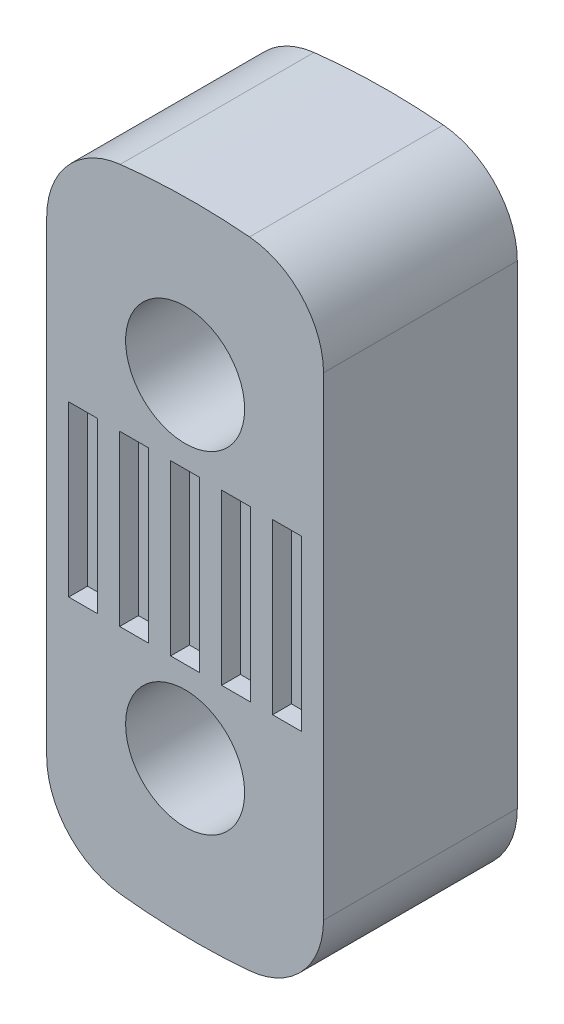
SolidWorks part; units mm, degrees
ref_plane "Front Plane" through (0, 0, 0) normal (0, 0, 1) x (1, 0, 0)
ref_plane "Top Plane" through (0, 0, 0) normal (0, 1, 0) x (1, 0, 0)
ref_plane "Right Plane" through (0, 0, 0) normal (1, 0, 0) x (0, 0, -1)
sketch "Sketch1" plane through (0, 0, 0) normal (0, 0, 1) x (1, 0, 0)
  line L0 (-34.3488, 6) -> (10.6512, 6) construction
  line L8 (-5, 14.4344) -> (-5, -2.4344)
  line L9 (5, 14.563) -> (5, -2.563)
  arc A0 (-2.3438, 17.4132) -> (-5, 14.4344) centre (-2.0016, 14.4344) ccw
  circle A1 centre (0, 0) radius 2.15
  arc A3 (0.0452, -5.5638) -> (-2.3438, -5.4132) centre (0.3138, 17.7221) cw
  arc A5 (5, 14.563) -> (2.3268, 17.4782) centre (2.0739, 14.563) ccw
  circle A6 centre (0, 12) radius 2.15
  arc A7 (2.3268, -5.4782) -> (0.0452, -5.5638) centre (0.3138, 17.7221) cw
  arc A8 (5, -2.563) -> (2.3268, -5.4782) centre (2.0739, -2.563) cw
  arc A9 (-2.3438, -5.4132) -> (-5, -2.4344) centre (-2.0016, -2.4344) cw
  arc A15 (2.3268, 17.4782) -> (0.0452, 17.5638) centre (0.3138, -5.7221) ccw
  arc A48 (0.0452, 17.5638) -> (-2.3438, 17.4132) centre (0.3138, -5.7221) ccw
extrude "Boss-Extrude1" add sketch "Sketch1" along normal blind 7
sketch "Sketch4" plane through (0, 0, 7) normal (0, 0, 1) x (1, 0, 0)
  line L0 (-4.2044, 9.0544) -> (-3.1591, 9.0544)
  line L2 (-2.3635, 9.0544) -> (-1.3182, 9.0544)
  line L5 (-0.5226, 9.0544) -> (0.5226, 9.0544)
  line L6 (-4.2044, 9.0544) -> (-4.2044, 2.9456)
  line L7 (1.3182, 9.0544) -> (2.3635, 9.0544)
  line L10 (3.1591, 9.0544) -> (4.2044, 9.0544)
  line L11 (4.2044, 2.9456) -> (3.1591, 2.9456)
  line L12 (2.3635, 2.9456) -> (1.3182, 2.9456)
  line L13 (-2.3635, 9.0544) -> (-2.3635, 2.9456)
  line L14 (0.5226, 2.9456) -> (-0.5226, 2.9456)
  line L15 (-3.1591, 9.0544) -> (-3.1591, 2.9456)
  line L16 (-1.3182, 2.9456) -> (-2.3635, 2.9456)
  line L17 (-0.5226, 9.0544) -> (-0.5226, 2.9456)
  line L18 (-3.1591, 2.9456) -> (-4.2044, 2.9456)
  line L19 (-1.3182, 9.0544) -> (-1.3182, 2.9456)
  line L21 (1.3182, 9.0544) -> (1.3182, 2.9456)
  line L23 (0.5226, 9.0544) -> (0.5226, 2.9456)
  line L25 (3.1591, 9.0544) -> (3.1591, 2.9456)
  line L27 (2.3635, 9.0544) -> (2.3635, 2.9456)
  line L31 (4.2044, 9.0544) -> (4.2044, 2.9456)
  line L33 (5, 9.0544) -> (5, 2.9456) [skipped]
  dimension "D2" = 6
extrude "Cut-Extrude2" cut sketch "Sketch4" against normal blind 0.68
